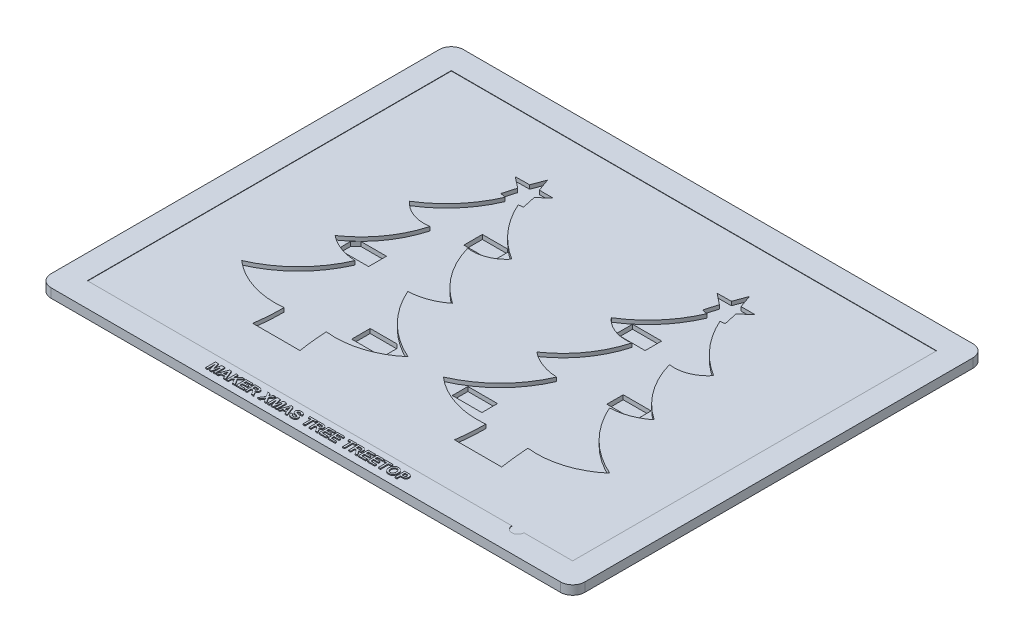
SolidWorks part; units mm, degrees
ref_plane "Front Plane" through (0, 0, 0) normal (0, 0, 1) x (1, 0, 0)
ref_plane "Top Plane" through (0, 0, 0) normal (0, 1, 0) x (1, 0, 0)
ref_plane "Right Plane" through (0, 0, 0) normal (1, 0, 0) x (0, 0, -1)
sketch "Sketch1" plane through (0, 0, 0) normal (0, 1, 0) x (1, 0, 0)
  line L1 (-105, 85) -> (105, 85)
  line L2 (-110, 80) -> (-110, -80)
  line L3 (-105, -85) -> (105, -85)
  line L4 (110, 80) -> (110, -80)
  line L5 (-110, 85) -> (110, -85) construction
  line L6 (-110, -85) -> (110, 85) construction
  arc A0 (-110, -80) -> (-105, -85) centre (-105, -80) ccw
  arc A1 (110, -80) -> (105, -85) centre (105, -80) cw
  arc A2 (110, 80) -> (105, 85) centre (105, 80) ccw
  arc A3 (-110, 80) -> (-105, 85) centre (-105, 80) cw
  point P0 (0, 0)
  dimension "D3" = 5
  dimension "D1" = 220
  dimension "D2" = 170
extrude "Boss-Extrude1" add sketch "Sketch1" along normal blind 3.75
sketch "Sketch2" plane through (0, 3.75, 0) normal (0, 1, 0) x (1, 0, 0)
  line L0 (79.9479, -75) -> (100, -75)
  line L1 (-100, 75) -> (100, 75)
  line L2 (-100, 75) -> (-100, -75)
  line L3 (-100, -75) -> (74.9479, -75)
  line L4 (100, 75) -> (100, -75)
  line L5 (-100, 75) -> (100, -75) construction
  line L6 (-100, -75) -> (100, 75) construction
  arc A0 (74.9479, -75) -> (79.9479, -75) centre (77.4479, -75) ccw
  point P0 (0, 0)
  dimension "D4" = 2.5
  dimension "D1" = 200
  dimension "D2" = 150
  dimension "D3" = 5
extrude "Cut-Extrude1" cut sketch "Sketch2" against normal blind 0.15
sketch "Sketch5" plane through (0, 3.75, 0) normal (0, 1, 0) x (1, 0, 0)
  text T0 "<b>MAKER XMAS TREE TREETOP</b>" font "Arial" height 4
extrude "Boss-Extrude2" add sketch "Sketch5" along normal blind 0.4
sketch "Sketch8" plane through (0, 3.6, 0) normal (0, 1, 0) x (1, 0, 0)
  line L0 (-44.5282, 46.8556) -> (-46.0647, 41.4851)
  line L1 (-46.0647, 41.4851) -> (-43.8946, 41.027)
  line L2 (-50.8705, -55.9788) -> (-45.783, -55.9788)
  line L3 (-45.783, -55.9788) -> (-45.783, -55.9666)
  line L9 (-36.917, -55.9666) -> (-36.917, -55.9663)
  line L10 (-36.917, -55.9663) -> (-31.4245, -55.9666)
  line L11 (-38.4758, 41.027) -> (-36.5497, 41.2699)
  line L12 (-36.5497, 41.2699) -> (-37.7509, 46.8556)
  line L13 (-37.7509, 46.8556) -> (-33.7938, 50.6204)
  line L14 (-33.7938, 50.6204) -> (-39.3604, 50.6204)
  line L15 (-39.3604, 50.6204) -> (-41.2492, 55.9162)
  line L16 (-41.2492, 55.9162) -> (-43.2553, 50.5289)
  line L17 (-43.2553, 50.5289) -> (-49.0959, 50.4646)
  line L18 (-49.0959, 50.4646) -> (-44.5282, 46.8556)
  line L38 (-45.783, -55.9666) -> (-36.917, -55.9666)
  line L40 (-41.2492, 55.9162) -> (-41.35, -55.9666) construction
  line L41 (32.2801, -55.9788) -> (37.3676, -55.9788)
  line L42 (38.6224, 46.8556) -> (37.0859, 41.4851)
  line L43 (46.6009, 41.2699) -> (45.3997, 46.8556)
  line L44 (49.3568, 50.6204) -> (43.7903, 50.6204)
  line L45 (46.2336, -55.9663) -> (51.7262, -55.9666)
  line L46 (41.9014, 55.9162) -> (39.8953, 50.5289)
  line L47 (41.9014, 55.9162) -> (41.8006, -55.9666) construction
  line L48 (45.3997, 46.8556) -> (49.3568, 50.6204)
  line L49 (46.2336, -55.9666) -> (46.2336, -55.9663)
  line L50 (37.3676, -55.9666) -> (46.2336, -55.9666)
  line L51 (44.6748, 41.027) -> (46.6009, 41.2699)
  line L52 (37.3676, -55.9788) -> (37.3676, -55.9666)
  line L53 (34.0548, 50.4646) -> (38.6224, 46.8556)
  line L54 (37.0859, 41.4851) -> (39.2561, 41.027)
  line L55 (43.7903, 50.6204) -> (41.9014, 55.9162)
  line L56 (39.8953, 50.5289) -> (34.0548, 50.4646)
  arc A0 (-62.1621, 19.9226) -> (-43.8946, 41.027) centre (-86.4542, 59.4076) ccw
  arc A1 (-62.1621, 19.9226) -> (-48.8981, 15.1385) centre (-51.2498, 29.3977) ccw
  arc A2 (-65.2522, -7.6765) -> (-48.8981, 15.1385) centre (-88.2004, 26.042) ccw
  arc A3 (-65.2522, -7.6765) -> (-52.2092, -12.5252) centre (-51.3915, 9.6416) ccw
  arc A4 (-75.573, -35.8445) -> (-52.2092, -12.5252) centre (-93.5634, 5.5441) ccw
  arc A5 (-75.573, -35.8445) -> (-50.0031, -43.9279) centre (-53.5051, -10.522) ccw
  arc A6 (-50.8705, -55.9788) -> (-50.0031, -43.9279) centre (-145.3226, -43.1235) ccw
  arc A7 (-32.7131, -43.8545) -> (-31.4245, -55.9666) centre (91.1608, -36.7998) ccw
  arc A8 (-32.7131, -43.8545) -> (-6.9625, -35.8941) centre (-28.9575, -10.374) ccw
  arc A9 (-30.3024, -12.6445) -> (-6.9625, -35.8941) centre (11.2489, 5.7283) ccw
  arc A10 (-30.3024, -12.6445) -> (-16.8564, -7.6765) centre (-31.1133, 10.2301) ccw
  arc A11 (-33.3968, 15.1385) -> (-16.8564, -7.6765) centre (5.8621, 26.1972) ccw
  arc A12 (-33.3968, 15.1385) -> (-20.3875, 20.3085) centre (-31.4245, 29.1283) ccw
  arc A13 (-38.4758, 41.027) -> (-20.3875, 20.3085) centre (4.283, 60.1022) ccw
  arc A28 (52.8482, -12.6445) -> (76.1881, -35.8941) centre (94.3996, 5.7283) ccw
  arc A29 (20.9886, 19.9226) -> (34.2525, 15.1385) centre (31.9008, 29.3977) ccw
  arc A30 (32.2801, -55.9788) -> (33.1475, -43.9279) centre (-62.172, -43.1235) ccw
  arc A31 (49.7538, 15.1385) -> (62.7631, 20.3085) centre (51.7262, 29.1283) ccw
  arc A32 (20.9886, 19.9226) -> (39.2561, 41.027) centre (-3.3035, 59.4076) ccw
  arc A33 (17.8985, -7.6765) -> (34.2525, 15.1385) centre (-5.0498, 26.042) ccw
  arc A34 (44.6748, 41.027) -> (62.7631, 20.3085) centre (87.4337, 60.1022) ccw
  arc A35 (7.5777, -35.8445) -> (30.9415, -12.5252) centre (-10.4128, 5.5441) ccw
  arc A36 (50.4375, -43.8545) -> (51.7262, -55.9666) centre (174.3114, -36.7998) ccw
  arc A37 (50.4375, -43.8545) -> (76.1881, -35.8941) centre (54.1932, -10.374) ccw
  arc A38 (49.7538, 15.1385) -> (66.2943, -7.6765) centre (89.0127, 26.1972) ccw
  arc A39 (52.8482, -12.6445) -> (66.2943, -7.6765) centre (52.0374, 10.2301) ccw
  arc A40 (17.8985, -7.6765) -> (30.9415, -12.5252) centre (31.7591, 9.6416) ccw
  arc A41 (7.5777, -35.8445) -> (33.1475, -43.9279) centre (29.6455, -10.522) ccw
  point P19 (0, 0)
  dimension "D1" = 49.1295
extrude "Cut-Extrude3" cut sketch "Sketch8" against normal blind 1.6
sketch "Sketch10" plane through (0, 2, 0) normal (0, 1, 0) x (1, 0, 0)
  line L5 (-61.5319, -8.9295) -> (-60.0918, -10.2596)
  line L6 (14.4077, -32.5828) -> (26.6036, -32.5828)
  line L11 (49.3678, -3.5313) -> (60.8915, -3.5313)
  line L12 (26.1075, 23.5607) -> (38.1172, 23.5607)
  line L17 (14.4077, -32.5828) -> (14.4077, -39.0302)
  line L18 (49.3678, -3.5313) -> (49.3678, -10.2596)
  line L25 (-26.5847, 24.6699) -> (-25.2732, 23.7895)
  line L27 (-61.5319, -5.0135) -> (-59.3831, -2.8711)
  line L28 (-15.4473, -32.0085) -> (-13.7608, -33.6525)
  line L34 (-26.4431, -32.0085) -> (-15.4473, -32.0085)
  line L38 (-26.4431, -32.0085) -> (-26.4431, -39.6358)
  line L43 (-36.8825, 24.6699) -> (-26.5847, 24.6699)
  line L56 (26.1075, 23.5607) -> (26.1075, 16.75)
  line L57 (26.1075, 16.75) -> (38.1172, 16.75)
  line L82 (-36.8825, 24.6699) -> (-36.8825, 17.0482)
  line L87 (38.1172, 23.5607) -> (38.1172, 16.75)
  line L88 (49.3678, -10.2596) -> (60.8915, -10.2596)
  line L93 (-26.4431, -39.6358) -> (-13.7608, -39.6358)
  line L94 (-13.7608, -33.6525) -> (-13.7608, -39.6358)
  line L95 (-36.8825, 17.0482) -> (-25.2732, 17.0482)
  line L96 (-25.2732, 23.7895) -> (-25.2732, 17.0482)
  line L97 (-48.8657, -10.2596) -> (-60.0918, -10.2596)
  line L98 (-48.8657, -10.2596) -> (-48.8657, -2.8711)
  line L99 (-48.8657, -2.8711) -> (-59.3831, -2.8711)
  line L100 (-61.5319, -8.9295) -> (-61.5319, -5.0135)
  line L101 (60.8915, -3.5313) -> (60.8915, -10.2596)
  line L102 (14.4077, -39.0302) -> (26.6036, -39.0302)
  line L103 (26.6036, -32.5828) -> (26.6036, -39.0302)
  arc A0 (-38.4758, 41.027) -> (-20.3875, 20.3085) centre (4.283, 60.1022) ccw construction
  point P12 (-56.144, -8.5021)
  point P36 (-29.2448, 18.7995)
  point P39 (0, 0)
  point P40 (0, 0)
  point P79 (-18.5964, -37.6198)
  point P80 (-56.144, -8.5021)
  point P81 (-29.2448, 18.7995)
  dimension "D1" = 10.2978
  dimension "D2" = 7.6218
  dimension "D3" = 11.6093
extrude "Cut-Extrude4" cut sketch "Sketch10" against normal blind 1.8
